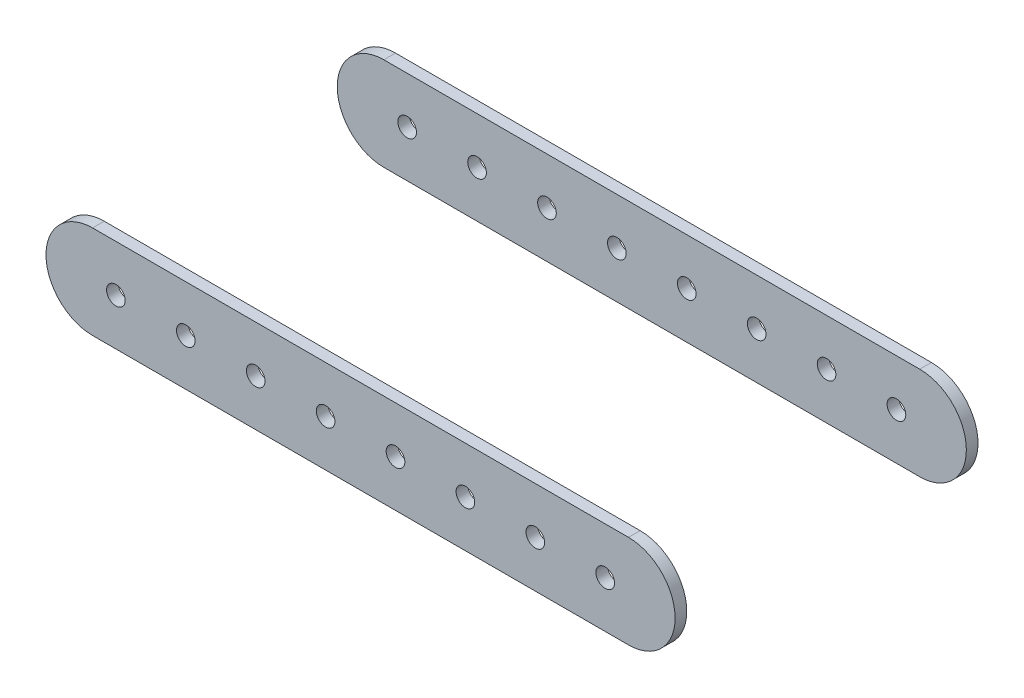
SolidWorks part; units mm, degrees
ref_plane "Plan de face" through (0, 0, 0) normal (0, 0, 1) x (1, 0, 0)
ref_plane "Plan de dessus" through (0, 0, 0) normal (0, 1, 0) x (1, 0, 0)
ref_plane "Plan de droite" through (0, 0, 0) normal (1, 0, 0) x (0, 0, -1)
sketch "Sketch1" plane through (0, 0, 0) normal (0, 0, 1) x (1, 0, 0)
  circle A0 centre (0, 0) radius 12.5
  circle A1 centre (0, 0) radius 4
  circle A2 centre (30, 0) radius 4
  circle A3 centre (30, 0) radius 12.5
  circle A4 centre (60, 0) radius 4
  circle A5 centre (60, 0) radius 12.5
  circle A6 centre (90, 0) radius 4
  circle A7 centre (90, 0) radius 12.5
  circle A8 centre (120, 0) radius 4
  circle A9 centre (120, 0) radius 12.5
  circle A10 centre (150, 0) radius 4
  circle A11 centre (150, 0) radius 12.5
  circle A12 centre (180, 0) radius 4
  circle A13 centre (180, 0) radius 12.5
  circle A14 centre (210, 0) radius 4
  circle A15 centre (210, 0) radius 12.5
  dimension "D1" = 25
  dimension "D2" = 8
ref_plane "Plane1" through (0, 0, 60) normal (0, 0, 1) x (1, 0, 0)
sketch "Sketch2" plane through (0, 0, 60) normal (0, 0, 1) x (1, 0, 0)
  line L0 (-10, 0) -> (220, 0) construction
  line L1 (-10, 20) -> (220, 20)
  line L2 (-10, -20) -> (220, -20)
  circle A0 centre (0, 0) radius 4
  circle A1 centre (210, 0) radius 4
  arc A2 (-10, 20) -> (-10, -20) centre (-10, 0) ccw
  arc A3 (220, -20) -> (220, 20) centre (220, 0) ccw
  point P8 (105, 0)
  dimension "D1" = 40
  dimension "D2" = 10
  dimension "D3" = 10
extrude "Boss-Extrude1" add sketch "Sketch2" along normal blind 5
mirror "Mirror5" about plane through (0, 0, 0) normal (0, 0, 1) of bodies 101
sketch "Sketch3" plane through (0, 0, 0) normal (0, 0, 1) x (1, 0, 0)
  circle A0 centre (210, 0) radius 4 construction
  circle A1 centre (180, 0) radius 4 construction
  circle A2 centre (150, 0) radius 4 construction
  circle A3 centre (120, 0) radius 4 construction
  circle A4 centre (90, 0) radius 4 construction
  circle A5 centre (60, 0) radius 4 construction
  circle A6 centre (30, 0) radius 4 construction
  circle A7 centre (0, 0) radius 4 construction
  circle A8 centre (210, 0) radius 4
  circle A9 centre (180, 0) radius 4
  circle A10 centre (150, 0) radius 4
  circle A11 centre (120, 0) radius 4
  circle A12 centre (90, 0) radius 4
  circle A13 centre (60, 0) radius 4
  circle A14 centre (30, 0) radius 4
  circle A15 centre (0, 0) radius 4
extrude "Cut-Extrude1" cut sketch "Sketch3" along normal through all and the other way through all
